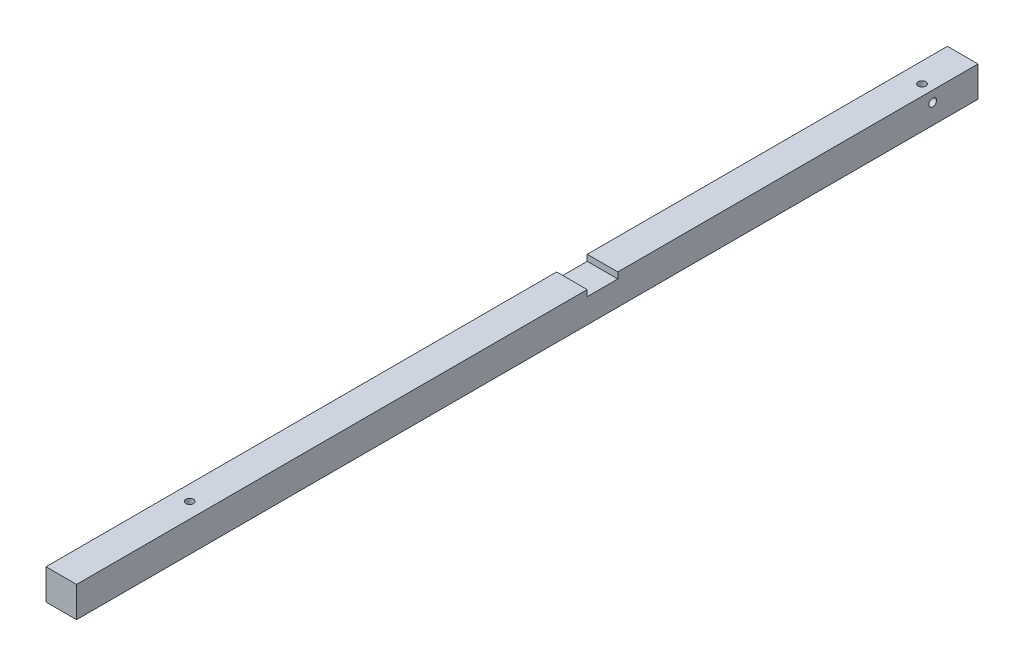
SolidWorks part; units mm, degrees
ref_plane "Plan de face" through (0, 0, 0) normal (0, 0, 1) x (1, 0, 0)
ref_plane "Plan de dessus" through (0, 0, 0) normal (0, 1, 0) x (1, 0, 0)
ref_plane "Plan de droite" through (0, 0, 0) normal (1, 0, 0) x (0, 0, -1)
sketch "Esquisse1" plane through (0, 0, 0) normal (0, 0, 1) x (1, 0, 0)
  line L0 (-5, 5) -> (5, -5) construction
  line L1 (-5, 5) -> (5, 5)
  line L2 (-5, 5) -> (-5, -5)
  line L3 (-5, -5) -> (5, -5)
  line L4 (5, 5) -> (5, -5)
  dimension "D1" = 10
extrude "Boss.-Extru.1" add sketch "Esquisse1" along normal offset from surface (294.8 mm away) 2
hole_wizard "Trou taraudé M3x0.51" positions "Esquisse3" profile "Esquisse2" tap size "M3x0.5" standard "Ansi Metric"
sketch "Esquisse3" plane through (0, 0, 0) normal (0, 0, -1) x (-1, 0, 0)
  point P0 (0, 0)
sketch "Esquisse2" plane through (0, 0, 0) normal (1, 0, 0) x (0, 1, 0)
  line L0 (0, 0) -> (0, 9.2511)
  line L1 (0, 9.2511) -> (1.25, 8.5)
  line L2 (1.25, 8.5) -> (1.25, 0.275)
  line L3 (1.25, 0.275) -> (1.525, 0)
  line L5 (1.525, 0) -> (0, 0)
  line L6 (-1.25, 0.275) -> (-1.525, 0) construction
  line L10 (0, 9.2511) -> (-1.25, 8.5) construction
  line L11 (0, -6.35) -> (0, 107.95) construction
  dimension "Diamètre du trou pour taraudage" = 2.5
  dimension "Profondeur du trou pour taraudage" = 8.5
  dimension "Diamètre du fraisage entrant" = 3.05
  dimension "Angle du fraisage entrant" = 90
  dimension "Angle de pointe" = 118
cosmetic thread "Filetage de perçage1" parameters "D1"=6, "D2"=3
sketch "Esquisse4" plane through (-5, 0, 0) normal (-1, 0, 0) x (0, 0, 1)
  line L0 (127.8, 3) -> (127.8, 239) construction
  line L1 (127.8, 3) -> (117.8, 3)
  line L2 (127.8, 3) -> (127.8, 5)
  line L3 (127.8, 5) -> (117.8, 5)
  line L4 (117.8, 3) -> (117.8, 5)
  line L5 (117.8, 3) -> (117.8, 239) construction
  line L6 (294.8, 5) -> (0, 5) construction
  dimension "D1" = 2
extrude "Enlèv. mat.-Extru.1" cut sketch "Esquisse4" against normal through all
sketch "Esquisse5" [suppressed] plane through (0, 5, 0) normal (0, 1, 0) x (1, 0, 0)
  line L0 (5, -294.8) -> (5, -127.8) construction
  line L1 (-5, 0) -> (5, 0)
  line L2 (-5, 0) -> (-5, -53.6)
  line L3 (-5, -53.6) -> (5, -53.6)
  line L4 (5, 0) -> (5, -53.6)
  line L5 (5, -117.8) -> (5, 0) construction
  line L6 (5, -53.6) -> (-5, -53.6) construction
hole_wizard "Trou taraudé M3x0.52" positions "Esquisse8" profile "Esquisse7" tap size "M3x0.5" standard "Ansi Metric" end condition through all
sketch "Esquisse8" plane through (0, -5, 0) normal (0, -1, 0) x (-1, 0, 0)
  point P0 (-1.5, -14.8)
sketch "Esquisse7" plane through (1.5, -5, 14.8) normal (1, 0, 0) x (0, 0, -1)
  line L0 (0, 0) -> (0, 10)
  line L1 (0, 10) -> (1.25, 10)
  line L2 (1.25, 10) -> (1.25, 0.275)
  line L3 (1.25, 0.275) -> (1.525, 0)
  line L5 (1.525, 0) -> (0, 0)
  line L6 (-1.25, 0.275) -> (-1.525, 0) construction
  line L11 (0, -6.35) -> (0, 107.95) construction
  dimension "Diamètre du trou pour taraudage jusqu'au prochain" = 2.5
  dimension "Profondeur du trou pour taraudage jusqu'au prochain" = 10
  dimension "Diamètre du fraisage entrant" = 3.05
  dimension "Angle du fraisage entrant" = 90
cosmetic thread "Filetage de perçage2" parameters "D2"=3
hole_wizard "Trou taraudé M3x0.53" positions "Esquisse10" profile "Esquisse9" tap size "M3x0.5" standard "Ansi Metric" end condition through all
sketch "Esquisse10" plane through (-5, 0, 0) normal (-1, 0, 0) x (0, 0, 1)
  point P0 (14.8, 1.5)
sketch "Esquisse9" plane through (-5, 1.5, 14.8) normal (0, 1, 0) x (0, 0, 1)
  line L0 (0, 0) -> (0, 10)
  line L1 (0, 10) -> (1.25, 10)
  line L2 (1.25, 10) -> (1.25, 0.275)
  line L3 (1.25, 0.275) -> (1.525, 0)
  line L5 (1.525, 0) -> (0, 0)
  line L6 (-1.25, 0.275) -> (-1.525, 0) construction
  line L11 (0, -6.35) -> (0, 107.95) construction
  dimension "Diamètre du trou pour taraudage jusqu'au prochain" = 2.5
  dimension "Profondeur du trou pour taraudage jusqu'au prochain" = 10
  dimension "Diamètre du fraisage entrant" = 3.05
  dimension "Angle du fraisage entrant" = 90
cosmetic thread "Filetage de perçage3" parameters "D2"=3
extrude "Enlèv. mat.-Extru.2" [suppressed] cut sketch "Esquisse5" against normal through all
hole_wizard "Trou taraudé M3x0.54" positions "Esquisse12" profile "Esquisse11" tap size "M3x0.5" standard "Ansi Metric" end condition through all
sketch "Esquisse12" plane through (0, -5, 0) normal (0, -1, 0) x (-1, 0, 0)
  point P0 (0, -252.8)
sketch "Esquisse11" plane through (0, -5, 252.8) normal (1, 0, 0) x (0, 0, -1)
  line L0 (0, 0) -> (0, 10)
  line L1 (0, 10) -> (1.25, 10)
  line L2 (1.25, 10) -> (1.25, 0.275)
  line L3 (1.25, 0.275) -> (1.525, 0)
  line L5 (1.525, 0) -> (0, 0)
  line L6 (-1.25, 0.275) -> (-1.525, 0) construction
  line L11 (0, -6.35) -> (0, 107.95) construction
  dimension "Diamètre du trou pour taraudage jusqu'au prochain" = 2.5
  dimension "Profondeur du trou pour taraudage jusqu'au prochain" = 10
  dimension "Diamètre du fraisage entrant" = 3.05
  dimension "Angle du fraisage entrant" = 90
cosmetic thread "Filetage de perçage5" parameters "D1"=10, "D2"=3
